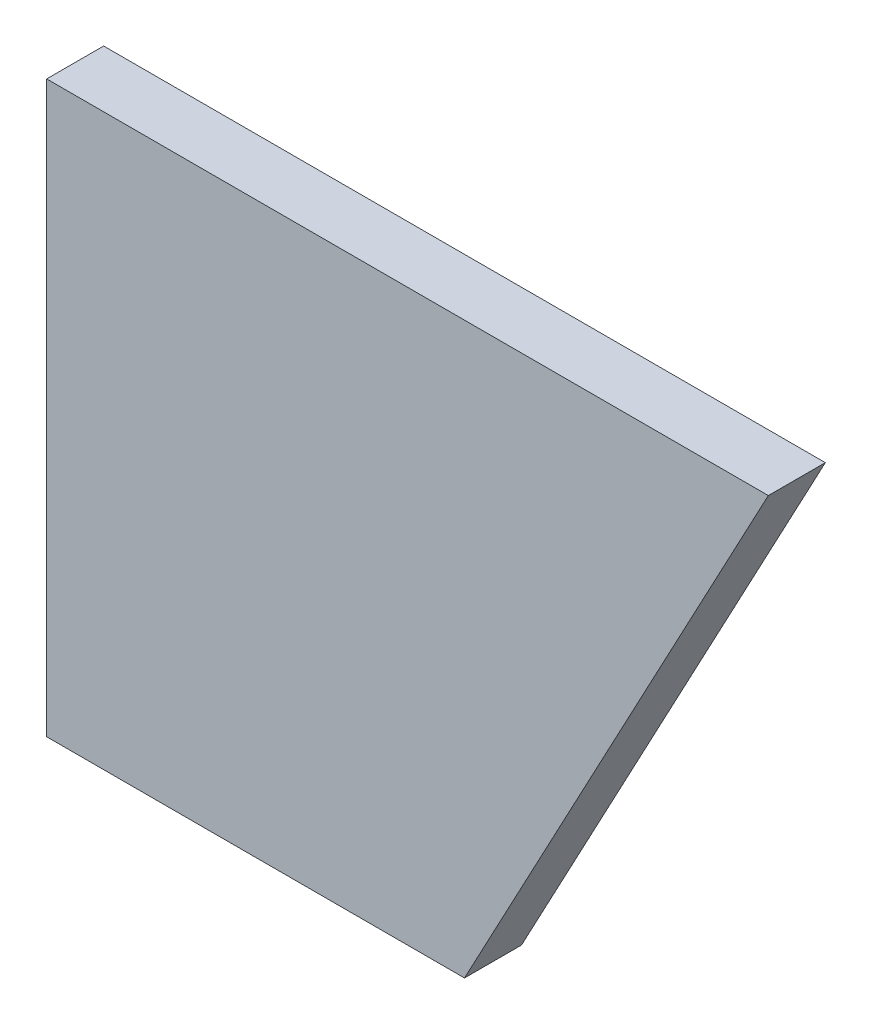
SolidWorks part; units mm, degrees
material "AISI 1020"
ref_plane "Plano frontal" through (0, 0, 0) normal (0, 0, 1) x (1, 0, 0)
ref_plane "Plano superior" through (0, 0, 0) normal (0, 1, 0) x (1, 0, 0)
ref_plane "Plano direito" through (0, 0, 0) normal (1, 0, 0) x (0, 0, -1)
sketch "Esboço1" plane through (0, 0, 0) normal (0, 0, 1) x (1, 0, 0)
  line L0 (0, 0) -> (22, 0)
  line L1 (0, 0) -> (0, 30)
  line L2 (0, 30) -> (38, 30)
  line L3 (38, 30) -> (22, 0)
  dimension "D1" = 38
  dimension "D2" = 30
  dimension "D3" = 22
  dimension "D4" = 30
extrude "Ressalto-extrusão1" add sketch "Esboço1" along normal blind 3
sketch "Esboço2" plane through (0, 0, 3) normal (0, 0, 1) x (1, 0, 0)
